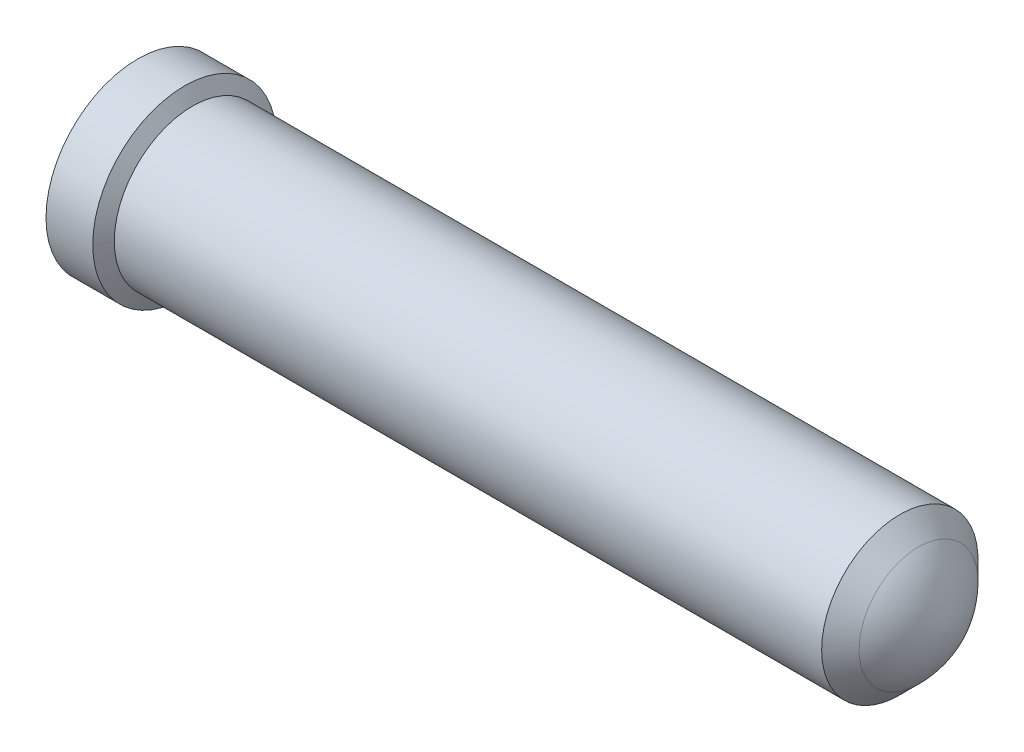
SolidWorks part; units mm, degrees
material "Brass Alloy 385"
ref_plane "Front Plane" through (0, 0, 0) normal (0, 0, 1) x (1, 0, 0)
ref_plane "Top Plane" through (0, 0, 0) normal (0, 1, 0) x (1, 0, 0)
ref_plane "Right Plane" through (0, 0, 0) normal (1, 0, 0) x (0, 0, -1)
sketch "Sketch1" plane through (0, 0, 0) normal (0, 0, 1) x (1, 0, 0)
  line L0 (0, 0) -> (0, 0.6236)
  line L1 (0, 0.6236) -> (0.3175, 0.6236)
  line L2 (0.3175, 0.6236) -> (0.371, 0.5309)
  line L3 (5.175, 0.5309) -> (0.371, 0.5309)
  line L4 (5.175, 0.5309) -> (5.302, 0.4039)
  line L5 (0, 0) -> (5.4864, 0)
  line L6 (0, 0) -> (5.4864, 0) construction
  arc A0 (5.4864, 0) -> (5.302, 0.4039) centre (4.853, -0.0452) ccw
revolve "RevolutionAngle1" add sketch "Sketch1" angle 360 about L6
hole_wizard "Hole1" positions "Sketch3" profile "Sketch2" legacy
sketch "Sketch3" plane through (0, 0, 0) normal (-1, 0, 0) x (0, 0, 1)
  point P0 (0, 0)
sketch "Sketch2" plane through (0, 0, 0) normal (0, 1, 0) x (0, 0, 1)
  line L0 (0, 0) -> (0, 1.7987)
  line L1 (0, 1.7987) -> (0.4572, 1.524)
  line L2 (0.4572, 1.524) -> (0.4572, 0.0889)
  line L3 (0.4572, 0.0889) -> (0.5461, 0)
  line L4 (0.5461, 0) -> (0, 0)
  line L5 (0, -14.3089) -> (0, 102.4216) construction
  line L6 (0, 1.7987) -> (-0.4572, 1.524) construction
  line L7 (-0.4572, 0.0889) -> (-0.5461, 0) construction
  dimension "Diameter" = 0.9144
  dimension "Depth" = 1.524
  dimension "C-Sink Diameter" = 1.0922
  dimension "C-Sink Angle" = 90
  dimension "Drill Angle" = 118
hole_wizard "Hole2" positions "3DSketch1" profile "Sketch4" legacy
sketch3d "3DSketch1"
  line L0 (0.3175, 0, 0) -> (0, 0, 0) construction
  point P0 (0, 0, 0)
sketch "Sketch4" plane through (0, 0, 0) normal (0, 1, 0) x (0, 0, 1)
  line L0 (0, 0) -> (0, 2.2051)
  line L1 (0, 2.2051) -> (0.4572, 1.9304)
  line L2 (0.4572, 1.9304) -> (0.4572, 0.0889)
  line L3 (0.4572, 0.0889) -> (0.5461, 0)
  line L4 (0.5461, 0) -> (0, 0)
  line L5 (0, -14.3089) -> (0, 102.4216) construction
  line L6 (0, 2.2051) -> (-0.4572, 1.9304) construction
  line L7 (-0.4572, 0.0889) -> (-0.5461, 0) construction
  dimension "Diameter" = 0.9144
  dimension "Depth" = 1.9304
  dimension "C-Sink Diameter" = 1.0922
  dimension "C-Sink Angle" = 90
  dimension "Drill Angle" = 118
